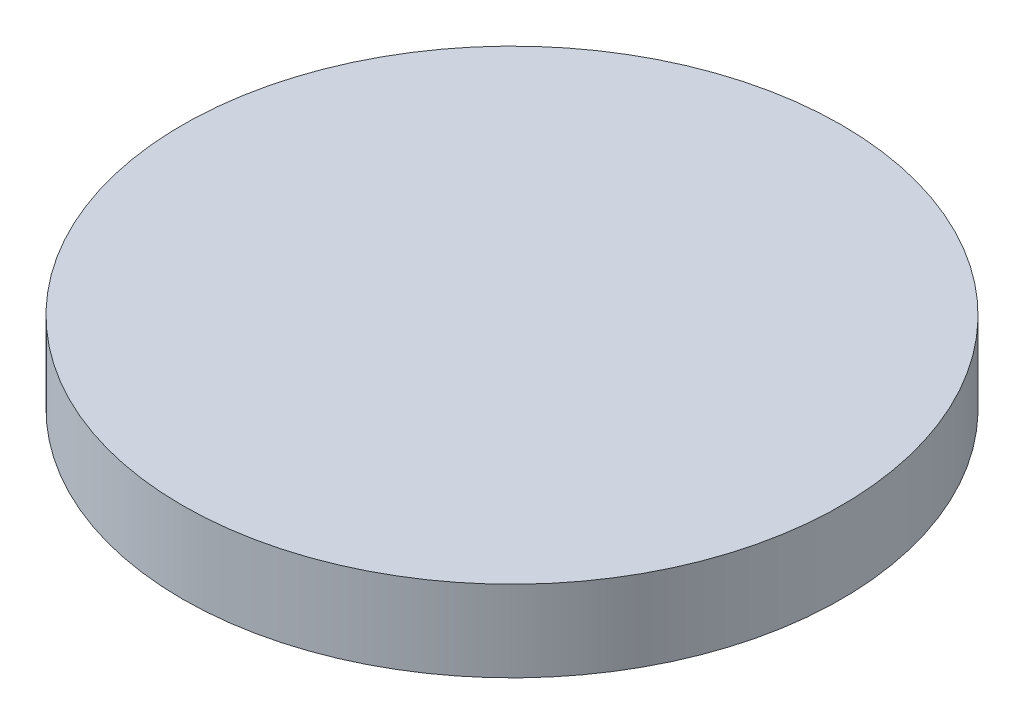
SolidWorks part; units mm, degrees
material "Glass"
ref_plane "Front Plane" through (0, 0, 0) normal (0, 0, 1) x (1, 0, 0)
ref_plane "Top Plane" through (0, 0, 0) normal (0, 1, 0) x (1, 0, 0)
ref_plane "Right Plane" through (0, 0, 0) normal (1, 0, 0) x (0, 0, -1)
sketch "Sketch1" plane through (0, 0, 0) normal (0, 1, 0) x (1, 0, 0)
  circle A0 centre (0, 0) radius 101.6
other "Pen Sketch1" parameters "D1"=33.0285
extrude "Boss-Extrude1" add sketch "Sketch1" along normal blind 25
